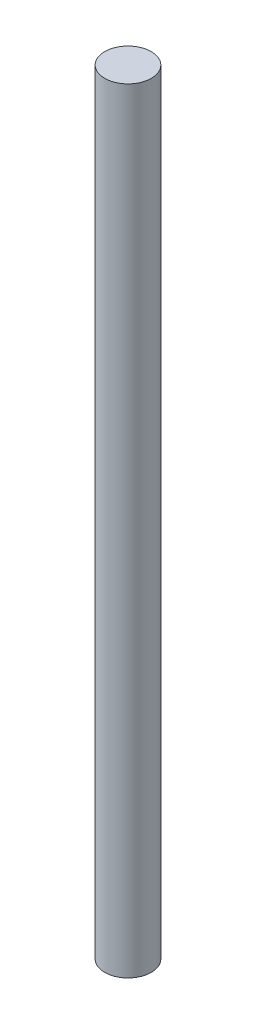
SolidWorks part; units mm, degrees
ref_plane "Front Plane" through (0, 0, 0) normal (0, 0, 1) x (1, 0, 0)
ref_plane "Top Plane" through (0, 0, 0) normal (0, 1, 0) x (1, 0, 0)
ref_plane "Right Plane" through (0, 0, 0) normal (1, 0, 0) x (0, 0, -1)
sketch "Sketch1" plane through (0, 0, 0) normal (0, 1, 0) x (1, 0, 0)
  circle A0 centre (0, 0) radius 1.5
  dimension "D1" = 3
extrude "Boss-Extrude1" add sketch "Sketch1" along normal blind 50
